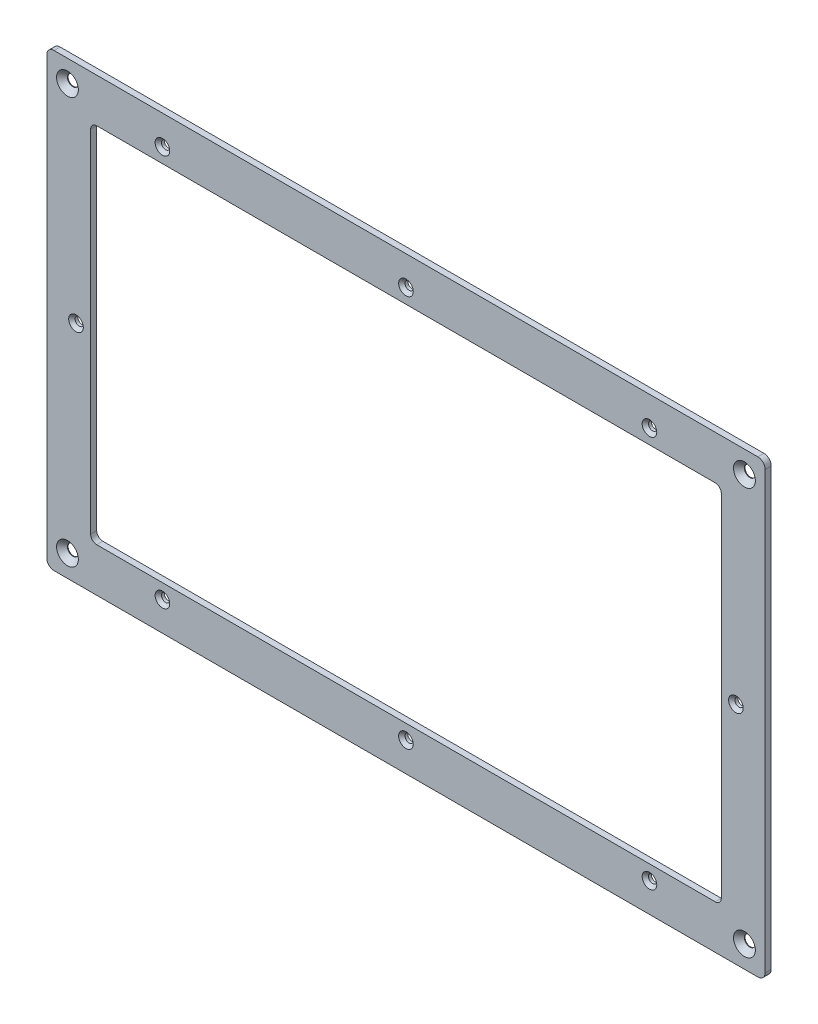
SolidWorks part; units mm, degrees
material "7079 Alloy"
ref_plane "Front" through (0, 0, 0) normal (0, 0, 1) x (1, 0, 0)
ref_plane "Top" through (0, 0, 0) normal (0, 1, 0) x (1, 0, 0)
ref_plane "Right" through (0, 0, 0) normal (1, 0, 0) x (0, 0, -1)
sketch "Sketch1" plane through (0, 0, 0) normal (0, 0, 1) x (1, 0, 0)
  line L0 (147.5, -92.5) -> (-147.5, 92.5) construction
  line L1 (-144.5, 92.5) -> (144.5, 92.5)
  line L2 (-147.5, 89.5) -> (-147.5, -89.5)
  line L3 (-144.5, -92.5) -> (144.5, -92.5)
  line L4 (147.5, 89.5) -> (147.5, -89.5)
  arc A0 (147.5, -89.5) -> (144.5, -92.5) centre (144.5, -89.5) cw
  arc A1 (144.5, 92.5) -> (147.5, 89.5) centre (144.5, 89.5) cw
  arc A2 (-147.5, 89.5) -> (-144.5, 92.5) centre (-144.5, 89.5) cw
  arc A3 (-144.5, -92.5) -> (-147.5, -89.5) centre (-144.5, -89.5) cw
  point P10 (147.5, 92.5)
  point P16 (-147.5, -92.5)
  dimension "D3" = 3
  dimension "D1" = 295
  dimension "D2" = 185
extrude "Extrude1" add sketch "Sketch1" along normal mid plane 2.5
sketch "Sketch5" plane through (0, 0, 1.25) normal (0, 0, 1) x (1, 0, 0)
  line L0 (129.5, -74.5) -> (-129.5, 74.5) construction
  line L1 (-127, 74.5) -> (127, 74.5)
  line L2 (-129.5, 72) -> (-129.5, -72)
  line L3 (-127, -74.5) -> (127, -74.5)
  line L4 (129.5, 72) -> (129.5, -72)
  line L5 (144.5, 92.5) -> (-144.5, 92.5) construction
  line L6 (-147.5, 89.5) -> (-147.5, -89.5) construction
  arc A0 (129.5, 72) -> (127, 74.5) centre (127, 72) ccw
  arc A1 (129.5, -72) -> (127, -74.5) centre (127, -72) cw
  arc A2 (-127, -74.5) -> (-129.5, -72) centre (-127, -72) cw
  arc A3 (-129.5, 72) -> (-127, 74.5) centre (-127, 72) cw
  dimension "D3" = 2.5
  dimension "D1" = 18
  dimension "D2" = 18
extrude "Cut-Extrude4" cut sketch "Sketch5" against normal through all
hole_wizard "Escareado para SFHCS M41" positions "Esboço2" profile "Esboço1" countersink size "M4" standard "Métrico Ansi" end condition through all
sketch "Esboço2" plane through (0, 0, 1.25) normal (0, 0, 1) x (1, 0, 0)
  line L0 (147.5, -89.5) -> (147.5, 89.5) construction
  line L1 (144.5, 92.5) -> (-144.5, 92.5) construction
  point P0 (139, 83.5)
  dimension "D1" = 8.5
  dimension "D2" = 9
sketch "Esboço1" plane through (139, 83.5, 1.25) normal (1, 0, 0) x (0, -1, 0)
  line L0 (0, 0) -> (0, 2.5)
  line L1 (0, 2.5) -> (2.25, 2.5)
  line L2 (2.25, 2.5) -> (2.25, 2.23)
  line L3 (2.25, 2.23) -> (4.48, 0)
  line L5 (4.48, 0) -> (0, 0)
  line L6 (-2.25, 2.23) -> (-4.48, 0) construction
  line L11 (0, -6.35) -> (0, 107.95) construction
  dimension "Thru Hole Dia." = 4.5
  dimension "Thru Hole Depth" = 2.5
  dimension "Near C'Sink Dia." = 8.96
  dimension "Near C'Sink Angle" = 90
hole_wizard "Furo com folga de M31" positions "Esboço4" profile "Esboço3" hole size "M3" standard "ISO" end condition through all
sketch "Esboço4" plane through (0, 0, 1.25) normal (0, 0, 1) x (1, 0, 0)
  line L1 (-147.5, 89.5) -> (-147.5, -89.5) construction
  line L2 (-144.5, -92.5) -> (144.5, -92.5) construction
  line L3 (147.5, -89.5) -> (147.5, 89.5) construction
  point P0 (0, -80.5)
  point P1 (-100, -80.5)
  point P3 (100, -80.5)
  point P6 (-135.5, 0)
  point P8 (135.5, 0)
  dimension "D1" = 12
  dimension "D2" = 12
  dimension "D3" = 12
  dimension "D4" = 12
  dimension "D5" = 12
  dimension "D6" = 100
  dimension "D7" = 100
sketch "Esboço3" plane through (0, -80.5, 1.25) normal (1, 0, 0) x (0, -1, 0)
  line L0 (0, 0) -> (0, 2.5)
  line L1 (0, 2.5) -> (1.7, 2.5)
  line L2 (1.7, 2.5) -> (1.7, 1.3)
  line L3 (1.7, 1.3) -> (3, 0)
  line L5 (3, 0) -> (0, 0)
  line L6 (-1.7, 1.3) -> (-3, 0) construction
  line L11 (0, -6.35) -> (0, 107.95) construction
  dimension "Thru Hole Dia." = 3.4
  dimension "Thru Hole Depth" = 2.5
  dimension "Near C'Sink Dia." = 6
  dimension "Near C'Sink Angle" = 90
mirror "Espelhar1" about plane through (0, 0, 0) normal (0, 1, 0) of "Furo com folga de M31"
mirror "Espelhar2" about plane through (0, 0, 0) normal (1, 0, 0) of "Escareado para SFHCS M41"
mirror "Espelhar3" about plane through (0, 0, 0) normal (0, 1, 0) of "Escareado para SFHCS M41", "Espelhar2"
